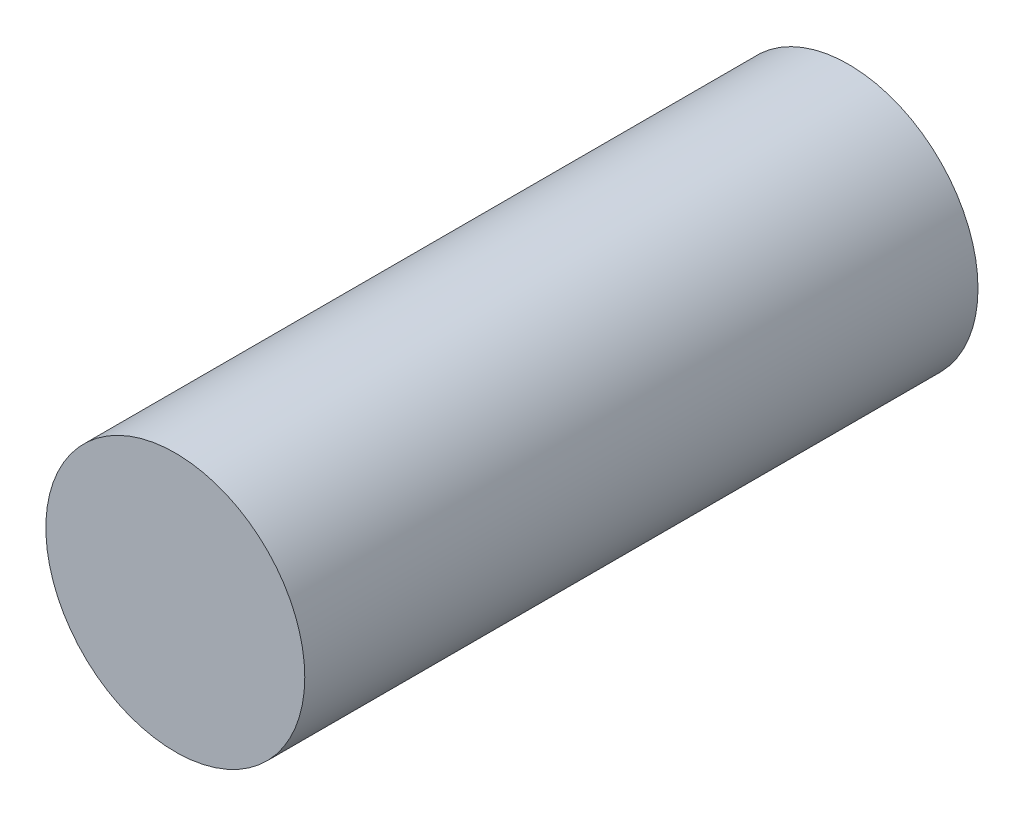
SolidWorks part; units mm, degrees
material "PET"
ref_plane "Front Plane" through (0, 0, 0) normal (0, 0, 1) x (1, 0, 0)
ref_plane "Top Plane" through (0, 0, 0) normal (0, 1, 0) x (1, 0, 0)
ref_plane "Right Plane" through (0, 0, 0) normal (1, 0, 0) x (0, 0, -1)
sketch "Sketch1" plane through (0, 0, 0) normal (0, 0, 1) x (1, 0, 0)
  circle A0 centre (0, 0) radius 2.5
  dimension "D1" = 5
extrude "Boss-Extrude1" add sketch "Sketch1" along normal blind 13
